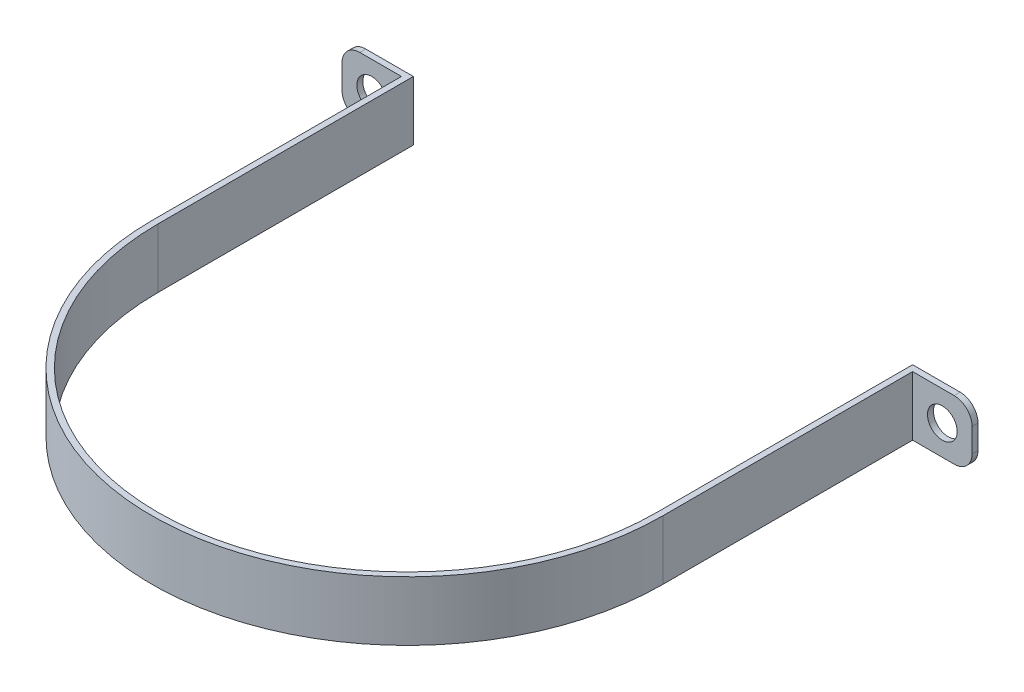
SolidWorks part; units mm, degrees
material "6061-T6 (SS)"
ref_plane "Płaszczyzna przednia" through (0, 0, 0) normal (0, 0, 1) x (1, 0, 0)
ref_plane "Płaszczyzna górna" through (0, 0, 0) normal (0, 1, 0) x (1, 0, 0)
ref_plane "Płaszczyzna prawa" through (0, 0, 0) normal (1, 0, 0) x (0, 0, -1)
sketch "Szkic2" plane through (0, 0, 0) normal (0, 1, 0) x (1, 0, 0)
  line L0 (-43, 43) -> (-42, 43)
  line L1 (42, 43) -> (43, 43)
  line L2 (-43, 0) -> (-43, 43)
  line L5 (-42, 0) -> (-42, 43)
  line L7 (43, 0) -> (43, 43)
  line L8 (42, 43) -> (42, 0)
  arc A0 (-42, 0) -> (42, 0) centre (0, 0) ccw
  arc A1 (-43, 0) -> (43, 0) centre (0, 0) ccw
  dimension "D1" = 1
  dimension "D3" = 42
  dimension "D2" = 43
extrude "Dodanie-wyciągnięcie1" add sketch "Szkic2" along normal blind 10
sketch "Szkic3" plane through (0, 0, -43) normal (0, 0, -1) x (-1, 0, 0)
  line L0 (-43, 10) -> (-53, 10)
  line L1 (-53, 10) -> (-53, 0)
  line L2 (-53, 0) -> (-43, 0)
  line L4 (-43, 10) -> (-43, 0)
  dimension "D1" = 10
  dimension "D2" = 10
extrude "Dodanie-wyciągnięcie2" add sketch "Szkic3" against normal blind 1
fillet "Zaokrąglenie1" radius 3 1 edges at (53, 10, -42.5)
fillet "Zaokrąglenie2" radius 3 1 edges at (53, 0, -42.5)
sketch "Szkic5" plane through (0, 0, -43) normal (0, 0, -1) x (-1, 0, 0)
  line L0 (-50, 0) -> (-42, 0) construction
  line L2 (-53, 7) -> (-53, 3) construction
  line L3 (-53, 5) -> (-48, 5)
  circle A0 centre (-48, 5) radius 2.5
  point P6 (-48, 5)
  dimension "D3" = 5
  dimension "D1" = 5
  dimension "D2" = 5
extrude "Wytnij-wyciągnięcie1" cut sketch "Szkic5" against normal blind 1 contours A0
mirror "Lustro1" about plane through (0, 0, 0) normal (1, 0, 0) of "Dodanie-wyciągnięcie2", "Zaokrąglenie1", "Zaokrąglenie2", "Wytnij-wyciągnięcie1"
